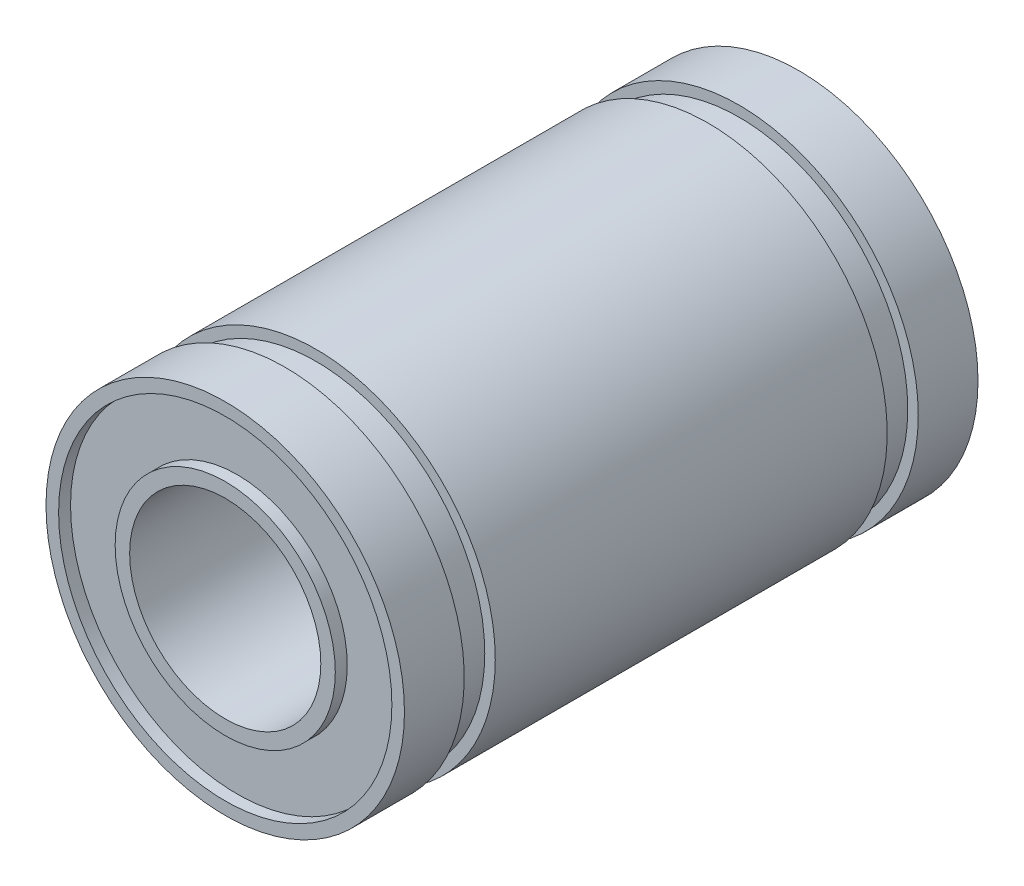
SolidWorks part; units mm, degrees
other "Camera2"
ref_plane "Front Plane" through (0, 0, 0) normal (0, 0, 1) x (1, 0, 0)
ref_plane "Top Plane" through (0, 0, 0) normal (0, 1, 0) x (1, 0, 0)
ref_plane "Right Plane" through (0, 0, 0) normal (1, 0, 0) x (0, 0, -1)
sketch "Sketch1" plane through (0, 0, 0) normal (0, 0, 1) x (1, 0, 0)
  circle A0 centre (0, 0) radius 7.5
  circle A1 centre (0, 0) radius 4
  dimension "D1" = 8
  dimension "D2" = 15
extrude "Boss-Extrude1" add sketch "Sketch1" along normal mid plane 24
sketch "Sketch2" plane through (0, 0, 0) normal (0, 1, 0) x (1, 0, 0)
  line L0 (0, 13.647) -> (0, -12.9935) construction
  line L1 (0, 0) -> (16.1989, 0) construction
  line L2 (7.0605, -9.5) -> (7.0605, -8.2)
  line L3 (7.9946, 9.5) -> (7.0605, 9.5)
  line L4 (7.9946, 9.5) -> (7.9946, 8.2)
  line L5 (7.9946, 8.2) -> (7.0605, 8.2)
  line L6 (7.0605, 9.5) -> (7.0605, 8.2)
  line L7 (7.9946, -8.2) -> (7.0605, -8.2)
  line L8 (7.9946, -9.5) -> (7.9946, -8.2)
  line L9 (7.9946, -9.5) -> (7.0605, -9.5)
  line L10 (7.5, 12) -> (-7.5, 12) construction
  dimension "D1" = 2.5
  dimension "D2" = 1.3
revolve "Cut-Revolve1" cut sketch "Sketch2" angle 360 about L0
sketch "Sketch3" plane through (0, 0, -12) normal (0, 0, -1) x (-1, 0, 0)
  circle A0 centre (0, 0) radius 4.6064
  circle A1 centre (0, 0) radius 6.9729
extrude "Cut-Extrude1" cut sketch "Sketch3" against normal blind 0.5
mirror "Mirror1" about plane through (0, 0, 0) normal (0, 0, 1) of "Cut-Extrude1"
